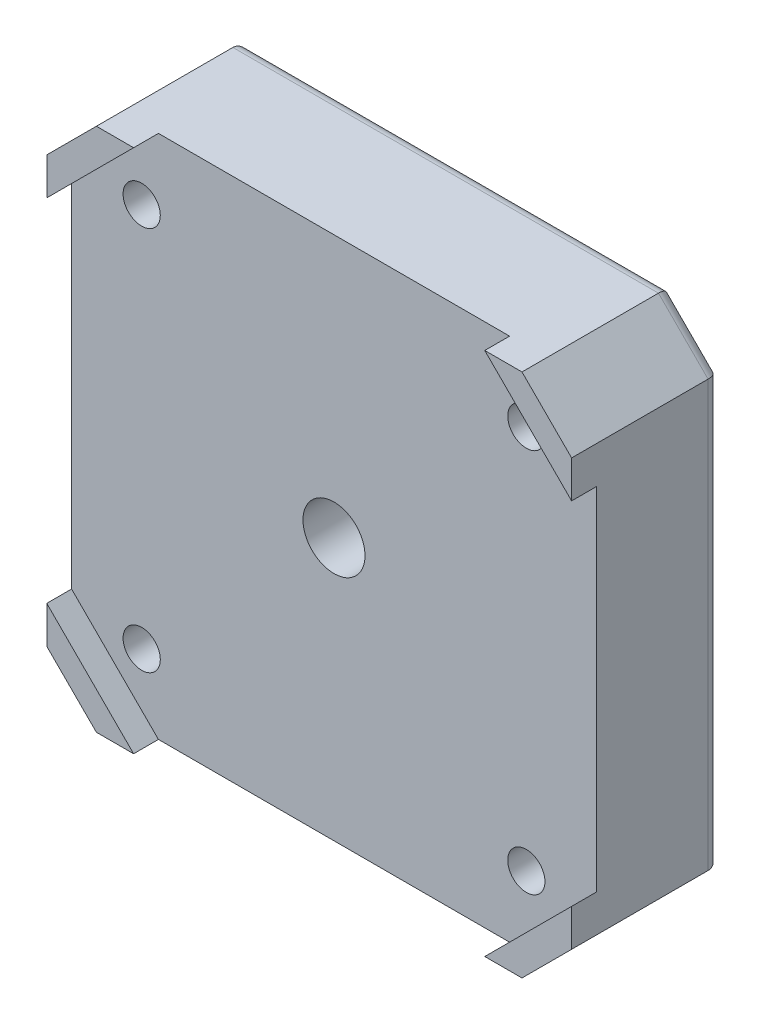
SolidWorks part; units mm, degrees
ref_plane "Front Plane" through (0, 0, 0) normal (0, 0, 1) x (1, 0, 0)
ref_plane "Top Plane" through (0, 0, 0) normal (0, 1, 0) x (1, 0, 0)
ref_plane "Right Plane" through (0, 0, 0) normal (1, 0, 0) x (0, 0, -1)
sketch "Sketch1" plane through (0, 0, 0) normal (0, 0, 1) x (1, 0, 0)
  line L0 (0, 76.6) -> (8, 84.6)
  line L1 (8, 0) -> (76.6, 0)
  line L2 (0, 8) -> (0, 76.6)
  line L3 (8, 84.6) -> (76.6, 84.6)
  line L4 (84.6, 8) -> (84.6, 76.6)
  line L5 (76.6, 84.6) -> (84.6, 76.6)
  line L6 (76.6, 0) -> (84.6, 8)
  line L7 (0, 8) -> (8, 0)
  point P0 (0, 0)
  point P1 (84.6, 84.6)
  point P2 (0, 84.6)
  point P3 (84.6, 0)
  dimension "D1" = 84.6
  dimension "D2" = 84.6
extrude "Boss-Extrude1" add sketch "Sketch1" along normal blind 24
sketch "Sketch2" plane through (0, 0, 24) normal (0, 0, 1) x (1, 0, 0)
  line L0 (42.3, 84.6) -> (42.3, 0) construction
  line L5 (76.6, 84.6) -> (8, 84.6) construction
  line L6 (8, 0) -> (76.6, 0) construction
  line L7 (42.3, 0) -> (0, 42.3) construction
  line L8 (0, 76.6) -> (0, 8) construction
  line L9 (0, 42.3) -> (84.6, 42.3) construction
  line L10 (84.6, 8) -> (84.6, 76.6) construction
  line L11 (0, 70.6) -> (14, 84.6)
  line L12 (14, 0) -> (70.6, 0)
  line L13 (0, 14) -> (0, 70.6)
  line L14 (14, 84.6) -> (70.6, 84.6)
  line L15 (84.6, 14) -> (84.6, 70.6)
  line L16 (0, 0) -> (84.6, 84.6) construction
  line L17 (0, 84.6) -> (84.6, 0) construction
  line L18 (70.6, 84.6) -> (84.6, 70.6)
  line L19 (70.6, 0) -> (84.6, 14)
  line L20 (0, 14) -> (14, 0)
  point P12 (42.3, 42.3)
  dimension "D2" = 56.6
  dimension "D5" = 56.6
extrude "Cut-Extrude1" cut sketch "Sketch2" against normal blind 4
sketch "Sketch3" plane through (0, 0, 20) normal (0, 0, 1) x (1, 0, 0)
  line L0 (0, 0) -> (84.6, 84.6) construction
  line L1 (11.3, 11.3) -> (73.3, 11.3) construction
  line L2 (11.3, 11.3) -> (11.3, 73.3) construction
  line L3 (11.3, 73.3) -> (73.3, 73.3) construction
  line L4 (73.3, 11.3) -> (73.3, 73.3) construction
  line L5 (11.3, 11.3) -> (73.3, 73.3) construction
  line L6 (11.3, 73.3) -> (73.3, 11.3) construction
  circle A0 centre (11.3, 73.3) radius 3
  circle A1 centre (73.3, 73.3) radius 3
  circle A2 centre (73.3, 11.3) radius 3
  circle A3 centre (11.3, 11.3) radius 3
  point P0 (42.3, 42.3)
  dimension "D2" = 6
  dimension "D3" = 6
  dimension "D4" = 6
  dimension "D5" = 6
  dimension "D1" = 62
extrude "Cut-Extrude2" cut sketch "Sketch3" against normal through all
sketch "Sketch5" plane through (0, 0, 0) normal (0, 0, -1) x (-1, 0, 0)
  circle A0 centre (-73.3, 73.3) radius 6.2
  circle A1 centre (-11.3, 73.3) radius 6.2
  circle A2 centre (-11.3, 11.3) radius 6.2
  circle A3 centre (-73.3, 11.3) radius 6.2
  dimension "D1" = 12.4
  dimension "D2" = 12.4
  dimension "D3" = 12.4
  dimension "D4" = 12.4
extrude "Cut-Extrude3" cut sketch "Sketch5" against normal blind 3
fillet "Fillet1" radius 1 8 edges at (67.1, 11.3, 0) (67.1, 11.3, 3) (5.1, 11.3, 0) (5.1, 11.3, 3) (5.1, 73.3, 0) (5.1, 73.3, 3) (67.1, 73.3, 0) (67.1, 73.3, 3)
fillet "Fillet2" radius 2 8 edges at (4, 80.6, 0) (0, 42.3, 0) (4, 4, 0) (42.3, 0, 0) (80.6, 4, 0) (84.6, 42.3, 0) (80.6, 80.6, 0) (42.3, 84.6, 0)
sketch "Sketch6" plane through (0, 0, 0) normal (0, 0, -1) x (-1, 0, 0)
  line L0 (0, 42.3) -> (-84.6, 42.3) construction
  line L1 (0, 76.6) -> (0, 8) construction
  line L2 (-84.6, 8) -> (-84.6, 76.6) construction
  line L3 (-84.6, 42.3) -> (-42.3, 82.6) construction
  line L4 (-8.8284, 82.6) -> (-75.7716, 82.6) construction
  line L5 (-42.3, 82.6) -> (-42.3, 2) construction
  line L6 (-75.7716, 2) -> (-8.8284, 2) construction
  circle A0 centre (-42.3, 42.3) radius 11
  dimension "D1" = 22
extrude "Cut-Extrude4" cut sketch "Sketch6" against normal blind 10
sketch "Sketch7" plane through (0, 0, 10) normal (0, 0, -1) x (-1, 0, 0)
  circle A0 centre (-42.3, 42.3) radius 5
  dimension "D1" = 10
extrude "Cut-Extrude5" cut sketch "Sketch7" against normal through all
fillet "Fillet3" radius 2 2 edges at (31.3, 42.3, 0) (31.3, 42.3, 10)
